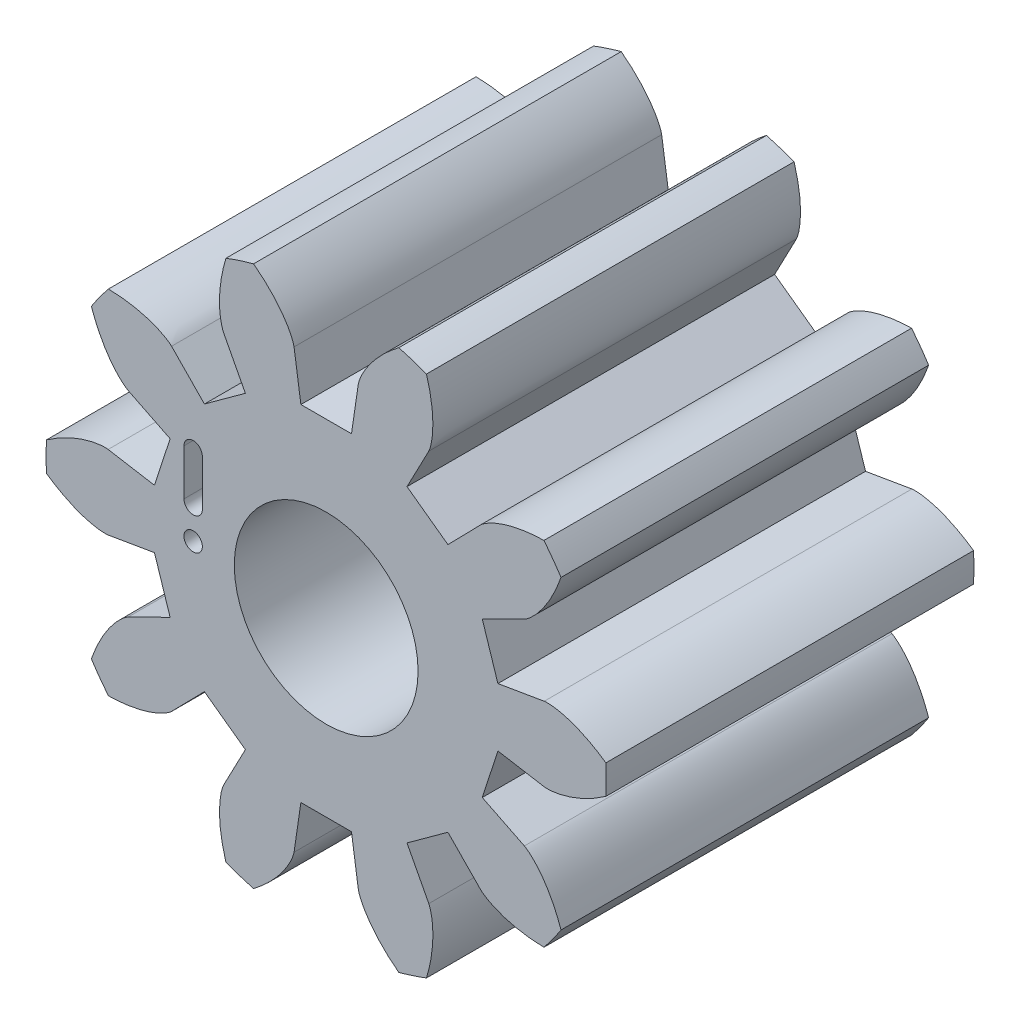
SolidWorks part; units mm, degrees
ref_plane "Front Plane" through (0, 0, 0) normal (0, 0, 1) x (1, 0, 0)
ref_plane "Top Plane" through (0, 0, 0) normal (0, 1, 0) x (1, 0, 0)
ref_plane "Right Plane" through (0, 0, 0) normal (1, 0, 0) x (0, 0, -1)
ref_axis "Axis1" through (0, 0, 4.2) along (0, 0, -1)
sketch "Sketch2" plane through (0, 0, 0) normal (0, 0, 1) x (1, 0, 0)
  circle A0 centre (0, 0) radius 3.0476
  dimension "D1" = 6.0951
extrude "Boss-Extrude1" add sketch "Sketch2" along normal blind 4
sketch "Sketch1" plane through (0, 0, 0) normal (0, 0, 1) x (1, 0, 0)
  line L1 (2.1564, 1.0683) -> (1.6982, 0.8413) construction
  line L3 (1.8683, 0.3175) -> (2.3725, 0.4032) construction
  line L4 (3.8854, 0) -> (4.3327, 0) construction
  line L8 (2.1564, 1.0683) -> (1.6982, 0.8413)
  line L9 (1.6982, 0.8413) -> (1.8683, 0.3175)
  line L10 (1.8683, 0.3175) -> (2.3725, 0.4032)
  circle A0 centre (0, 0) radius 1.8951 construction
  circle A1 centre (0, 0) radius 2.4065 construction
  circle A6 centre (0, 0) radius 3.0476 construction
  arc A7 (2.5994, 1.8069) -> (3.165, 0.0661) centre (0, 0) cw
  arc A8 (1.6982, 0.8413) -> (1.8683, 0.3175) centre (0, 0) cw construction
  circle A11 centre (0, 0) radius 3.0476 construction
  arc A12 (2.1564, 1.0683) -> (2.3725, 0.4032) centre (0, 0) cw construction
  spline S0 degree 4 poles (2.1564, 1.0683) (2.1596, 1.07) (2.1656, 1.0735) (2.1751, 1.0796) (2.1932, 1.0925) (2.2129, 1.1083) (2.2344, 1.1272) (2.2565, 1.1487) (2.2749, 1.1678) (2.2926, 1.1874) (2.3098, 1.2075) (2.3301, 1.2324) (2.3535, 1.2632) (2.3796, 1.3004) (2.4076, 1.344) (2.4345, 1.3898) (2.4596, 1.4361) (2.4833, 1.484) (2.505, 1.5313) (2.5258, 1.5816) (2.5441, 1.6286) (2.5626, 1.6825) (2.577, 1.7264) (2.5938, 1.7854) (2.6031, 1.8207) (2.6133, 1.8623) (2.6174, 1.881) (2.6199, 1.8925) knots 0 0 0 0 0 0.015084 0.028532 0.04661 0.092111 0.119476 0.146842 0.174209 0.201575 0.228941 0.256307 0.307035 0.361767 0.4165 0.471232 0.525964 0.580697 0.635429 0.690161 0.744894 0.799626 0.854358 0.909091 0.954545 1 1 1 1 1 construction
  spline S1 degree 4 poles (2.1564, 1.0683) (2.1596, 1.07) (2.1656, 1.0735) (2.1751, 1.0796) (2.1932, 1.0925) (2.2129, 1.1083) (2.2344, 1.1272) (2.2565, 1.1487) (2.2749, 1.1678) (2.2926, 1.1874) (2.3098, 1.2075) (2.3301, 1.2324) (2.3535, 1.2632) (2.3796, 1.3004) (2.4076, 1.344) (2.4345, 1.3898) (2.4596, 1.4361) (2.4833, 1.484) (2.505, 1.5313) (2.5258, 1.5816) (2.5441, 1.6286) (2.5626, 1.6825) (2.577, 1.7264) (2.5902, 1.7726) (2.5964, 1.7953) (2.5994, 1.8069) knots 0 0 0 0 0 0.015084 0.028532 0.04661 0.092111 0.119476 0.146842 0.174209 0.201575 0.228941 0.256307 0.307035 0.361767 0.4165 0.471232 0.525964 0.580697 0.635429 0.690161 0.744894 0.799626 0.854358 0.909091 0.909091 0.909091 0.909091 0.909091
  spline S2 degree 4 poles (2.3725, 0.4032) (2.3761, 0.4038) (2.383, 0.4044) (2.3942, 0.4051) (2.4165, 0.4053) (2.4417, 0.4041) (2.4702, 0.4014) (2.5007, 0.397) (2.5268, 0.3924) (2.5527, 0.387) (2.5784, 0.3808) (2.6095, 0.3725) (2.6465, 0.3614) (2.6895, 0.3466) (2.7378, 0.3279) (2.7865, 0.3066) (2.834, 0.2839) (2.8813, 0.259) (2.9266, 0.2335) (2.973, 0.2051) (3.0155, 0.1778) (3.0622, 0.1451) (3.0996, 0.1181) (3.1479, 0.0802) (3.1761, 0.0571) (3.2088, 0.0294) (3.2231, 0.0167) (3.2319, 0.0089) knots 0 0 0 0 0 0.015084 0.028532 0.04661 0.092111 0.119476 0.146842 0.174209 0.201575 0.228941 0.256307 0.307035 0.361767 0.4165 0.471232 0.525964 0.580697 0.635429 0.690161 0.744894 0.799626 0.854358 0.909091 0.954545 1 1 1 1 1 construction
  spline S3 degree 4 poles (2.3725, 0.4032) (2.3761, 0.4038) (2.383, 0.4044) (2.3942, 0.4051) (2.4165, 0.4053) (2.4417, 0.4041) (2.4702, 0.4014) (2.5007, 0.397) (2.5268, 0.3924) (2.5527, 0.387) (2.5784, 0.3808) (2.6095, 0.3725) (2.6465, 0.3614) (2.6895, 0.3466) (2.7378, 0.3279) (2.7865, 0.3066) (2.834, 0.2839) (2.8813, 0.259) (2.9266, 0.2335) (2.973, 0.2051) (3.0155, 0.1778) (3.0622, 0.1451) (3.0996, 0.1181) (3.1374, 0.0884) (3.1557, 0.0737) (3.165, 0.0661) knots 0 0 0 0 0 0.015084 0.028532 0.04661 0.092111 0.119476 0.146842 0.174209 0.201575 0.228941 0.256307 0.307035 0.361767 0.4165 0.471232 0.525964 0.580697 0.635429 0.690161 0.744894 0.799626 0.854358 0.909091 0.909091 0.909091 0.909091 0.909091
  dimension "D1" = 3.7902
  dimension "D2" = 4.8131
  dimension "D3" = 6.0951
  dimension "D4" = 6.0951
extrude "Cut-Extrude2" cut sketch "Sketch1" along normal through all
pattern_circular "CirPattern1" count 10 over 360 about axis through (0, 0, 4.2) along (0, 0, -1) of "Cut-Extrude2"
sketch "Sketch3" plane through (0, 0, 0) normal (0, 0, 1) x (1, 0, 0)
  circle A0 centre (0, 0) radius 1
  dimension "D1" = 2
extrude "Cut-Extrude3" cut sketch "Sketch3" along normal through all
sketch "Sketch4" plane through (0, 0, 0) normal (0, 0, 1) x (1, 0, 0)
  circle A0 centre (-1.4476, 0) radius 0.1
  spline S0 degree 1 poles (0, 0) (-1.4476, 0) knots 0 0 1 1 construction
  spline S1 degree 1 poles (0, 0) (-1.4476, 0) knots 0 0 1 1 construction
  dimension "D1" = 0.2
extrude "LocationCut" cut sketch "Sketch4" against normal through all both and the other way through all
sketch "Sketch5" [suppressed] plane through (0, 0, 0) normal (0, 0, 1) x (1, 0, 0)
  circle A0 centre (-0.4403, -1.3553) radius 0.1
  spline S0 degree 4 poles (0.0444, 0.1366) (0.0427, 0.1313) (0.0387, 0.1192) (0.0364, 0.112) (0.0216, 0.0664) (0.0029, 0.0091) (-0.0129, -0.0397) (-0.0535, -0.1648) (-0.0781, -0.2403) (-0.1122, -0.3454) (-0.1367, -0.4206) (-0.1626, -0.5004) (-0.1847, -0.5683) (-0.2079, -0.6399) (-0.2298, -0.7074) (-0.2509, -0.7721) (-0.2697, -0.83) (-0.287, -0.8833) (-0.3035, -0.9341) (-0.3206, -0.9868) (-0.3382, -1.0409) (-0.3537, -1.0887) (-0.3703, -1.1398) (-0.3839, -1.1816) (-0.4009, -1.2337) (-0.4134, -1.2722) (-0.4355, -1.3402) (-0.4438, -1.3658) (-0.4625, -1.4234) (-0.4697, -1.4456) (-0.4783, -1.4719) (-0.4812, -1.4811) (-0.4834, -1.4877) (-0.4845, -1.4911) knots 0 0 0 0 0 0.010417 0.020833 0.041667 0.083333 0.145671 0.208009 0.267342 0.324672 0.369982 0.413075 0.452591 0.497901 0.542139 0.581511 0.610383 0.640797 0.673373 0.705996 0.740957 0.77184 0.79428 0.826344 0.853073 0.883495 0.916667 0.947038 0.971084 0.985542 0.992771 1 1 1 1 1 construction
  spline S1 degree 4 poles (0, 0) (-0.0069, -0.0211) (-0.0204, -0.0628) (-0.0535, -0.1648) (-0.0781, -0.2403) (-0.1122, -0.3454) (-0.1367, -0.4206) (-0.1626, -0.5004) (-0.1847, -0.5683) (-0.2079, -0.6399) (-0.2298, -0.7074) (-0.2509, -0.7721) (-0.2697, -0.83) (-0.287, -0.8833) (-0.3035, -0.9341) (-0.3206, -0.9868) (-0.3382, -1.0409) (-0.3537, -1.0887) (-0.3703, -1.1398) (-0.3839, -1.1816) (-0.4009, -1.2337) (-0.4134, -1.2722) (-0.4299, -1.3231) (-0.4367, -1.344) (-0.4403, -1.3553) knots 0.083333 0.083333 0.083333 0.083333 0.083333 0.145671 0.208009 0.267342 0.324672 0.369982 0.413075 0.452591 0.497901 0.542139 0.581511 0.610383 0.640797 0.673373 0.705996 0.740957 0.77184 0.79428 0.826344 0.853073 0.883495 0.916667 0.916667 0.916667 0.916667 0.916667 construction
  dimension "D1" = 0.2
extrude "S2LocationCut" [suppressed] cut sketch "Sketch5" against normal through all both and the other way through all
sketch "Sketch6" [suppressed] plane through (0, 0, 0) normal (0, 0, 1) x (1, 0, 0)
  circle A0 centre (1.1528, -0.8376) radius 0.1
  spline S0 degree 4 poles (-0.1162, 0.0844) (-0.1123, 0.0816) (-0.1001, 0.0727) (-0.0972, 0.0706) (-0.0542, 0.0394) (-0.008, 0.0058) (0.038, -0.0276) (0.1475, -0.1072) (0.2176, -0.1581) (0.3138, -0.228) (0.3884, -0.2822) (0.4647, -0.3376) (0.5272, -0.383) (0.5888, -0.4278) (0.6415, -0.4661) (0.6953, -0.5052) (0.7461, -0.5421) (0.7915, -0.5751) (0.8356, -0.6071) (0.8793, -0.6389) (0.9216, -0.6696) (0.9631, -0.6998) (1.0029, -0.7287) (1.0349, -0.7519) (1.0719, -0.7788) (1.0978, -0.7976) (1.1431, -0.8305) (1.1645, -0.8461) (1.212, -0.8806) (1.229, -0.8929) (1.2544, -0.9114) (1.261, -0.9162) (1.2659, -0.9197) (1.2684, -0.9216) knots 0 0 0 0 0 0.010417 0.020833 0.041667 0.083333 0.14901 0.214686 0.279361 0.34003 0.394259 0.450635 0.487313 0.527902 0.568491 0.605347 0.641512 0.675567 0.699462 0.732706 0.768716 0.796045 0.822421 0.843371 0.867803 0.892235 0.916667 0.941265 0.9749 0.98745 0.993725 1 1 1 1 1 construction
  spline S1 degree 4 poles (0, 0) (0.0189, -0.0138) (0.0572, -0.0415) (0.1475, -0.1072) (0.2176, -0.1581) (0.3138, -0.228) (0.3884, -0.2822) (0.4647, -0.3376) (0.5272, -0.383) (0.5888, -0.4278) (0.6415, -0.4661) (0.6953, -0.5052) (0.7461, -0.5421) (0.7915, -0.5751) (0.8356, -0.6071) (0.8793, -0.6389) (0.9216, -0.6696) (0.9631, -0.6998) (1.0029, -0.7287) (1.0349, -0.7519) (1.0719, -0.7788) (1.0978, -0.7976) (1.1317, -0.8223) (1.1458, -0.8325) (1.1528, -0.8376) knots 0.083333 0.083333 0.083333 0.083333 0.083333 0.14901 0.214686 0.279361 0.34003 0.394259 0.450635 0.487313 0.527902 0.568491 0.605347 0.641512 0.675567 0.699462 0.732706 0.768716 0.796045 0.822421 0.843371 0.867803 0.892235 0.916667 0.916667 0.916667 0.916667 0.916667 construction
  dimension "D1" = 0.2
extrude "S3LocationCut" [suppressed] cut sketch "Sketch6" against normal through all both and the other way through all
sketch "Sketch7" plane through (0, 0, 4) normal (0, 0, 1) x (1, 0, 0)
  line L0 (-1.4476, 0.85) -> (-1.4476, 0.35) construction
  line L2 (-1.5476, 0.85) -> (-1.5476, 0.35)
  line L4 (-1.3476, 0.85) -> (-1.3476, 0.35)
  line L5 (-1.4476, 0.6) -> (-2.6866, 0.6) construction
  arc A0 (-1.5476, 0.85) -> (-1.3476, 0.85) centre (-1.4476, 0.85) cw
  arc A1 (-1.5476, 0.35) -> (-1.3476, 0.35) centre (-1.4476, 0.35) ccw
  spline S0 degree 1 poles (0, 0) (-1.4476, 0) knots 0 0 1 1 construction
  dimension "D1" = 0.2
  dimension "D2" = 0.5
  dimension "D3" = 0.6
extrude "Cut-Extrude4" cut sketch "Sketch7" against normal blind 0.2 and the other way through all
sketch "Sketch8" [suppressed] plane through (0, 0, 4) normal (0, 0, 1) x (1, 0, 0)
  line L0 (-0.9159, -1.2007) -> (-1.2012, -1.108) construction
  line L2 (-0.885, -1.1056) -> (-1.1703, -1.0129)
  line L4 (-0.9468, -1.2959) -> (-1.2321, -1.2031)
  line L5 (-1.3701, -2.1132) -> (-1.0585, -1.1544) construction
  line L6 (-1.0086, -1.4861) -> (-1.2939, -1.3934)
  line L7 (-1.0704, -1.6763) -> (-1.3557, -1.5836)
  line L8 (-1.0395, -1.5812) -> (-1.3248, -1.4885) construction
  arc A0 (-0.885, -1.1056) -> (-0.9468, -1.2959) centre (-0.9159, -1.2007) cw
  arc A1 (-1.1703, -1.0129) -> (-1.2321, -1.2031) centre (-1.2012, -1.108) ccw
  arc A2 (-1.0086, -1.4861) -> (-1.0704, -1.6763) centre (-1.0395, -1.5812) cw
  arc A3 (-1.2939, -1.3934) -> (-1.3557, -1.5836) centre (-1.3248, -1.4885) ccw
  spline S0 degree 4 poles (0, 0) (-0.0069, -0.0211) (-0.0204, -0.0628) (-0.0535, -0.1648) (-0.0781, -0.2403) (-0.1122, -0.3454) (-0.1367, -0.4206) (-0.1626, -0.5004) (-0.1847, -0.5683) (-0.2079, -0.6399) (-0.2298, -0.7074) (-0.2509, -0.7721) (-0.2697, -0.83) (-0.287, -0.8833) (-0.3035, -0.9341) (-0.3206, -0.9868) (-0.3382, -1.0409) (-0.3537, -1.0887) (-0.3703, -1.1398) (-0.3839, -1.1816) (-0.4009, -1.2337) (-0.4134, -1.2722) (-0.4299, -1.3231) (-0.4367, -1.344) (-0.4403, -1.3553) knots 0.083333 0.083333 0.083333 0.083333 0.083333 0.145671 0.208009 0.267342 0.324672 0.369982 0.413075 0.452591 0.497901 0.542139 0.581511 0.610383 0.640797 0.673373 0.705996 0.740957 0.77184 0.79428 0.826344 0.853073 0.883495 0.916667 0.916667 0.916667 0.916667 0.916667 construction
  dimension "D1" = 0.2
  dimension "D2" = 0.3
  dimension "D4" = 0.5
  dimension "D5" = 0.4
  dimension "D3" = 2
extrude "Cut-Extrude5" [suppressed] cut sketch "Sketch8" against normal blind 0.5
sketch "Sketch9" [suppressed] plane through (0, 0, 4) normal (0, 0, 1) x (1, 0, 0)
  line L0 (0.712, -1.4444) -> (1.0059, -1.0398) construction
  line L1 (0.7929, -1.5031) -> (1.0868, -1.0986)
  line L3 (0.6311, -1.3856) -> (0.925, -0.9811)
  line L4 (0.859, -1.2421) -> (0.7858, -1.189) construction
  line L5 (1.0356, -1.6795) -> (1.3295, -1.275)
  line L6 (0.8738, -1.5619) -> (1.1677, -1.1574)
  line L7 (0.9547, -1.6207) -> (1.2486, -1.2162) construction
  line L8 (0.5502, -1.3268) -> (0.8441, -0.9223)
  line L9 (0.3884, -1.2092) -> (0.6823, -0.8047)
  line L10 (0.4693, -1.268) -> (0.7632, -0.8635) construction
  line L11 (0.9547, -1.6207) -> (1.0356, -1.6795) construction
  line L12 (0.712, -1.4444) -> (0.7929, -1.5031) construction
  line L13 (0.4693, -1.268) -> (0.5502, -1.3268) construction
  line L14 (0.4693, -1.268) -> (0.712, -1.4444) construction
  line L15 (0.712, -1.4444) -> (0.9547, -1.6207) construction
  arc A0 (0.6311, -1.3856) -> (0.7929, -1.5031) centre (0.712, -1.4444) ccw
  arc A1 (0.925, -0.9811) -> (1.0868, -1.0986) centre (1.0059, -1.0398) cw
  arc A2 (0.8738, -1.5619) -> (1.0356, -1.6795) centre (0.9547, -1.6207) ccw
  arc A3 (1.1677, -1.1574) -> (1.3295, -1.275) centre (1.2486, -1.2162) cw
  arc A4 (0.3884, -1.2092) -> (0.5502, -1.3268) centre (0.4693, -1.268) ccw
  arc A5 (0.6823, -0.8047) -> (0.8441, -0.9223) centre (0.7632, -0.8635) cw
  spline S0 degree 4 poles (0, 0) (0.0189, -0.0138) (0.0572, -0.0415) (0.1475, -0.1072) (0.2176, -0.1581) (0.3138, -0.228) (0.3884, -0.2822) (0.4647, -0.3376) (0.5272, -0.383) (0.5888, -0.4278) (0.6415, -0.4661) (0.6953, -0.5052) (0.7461, -0.5421) (0.7915, -0.5751) (0.8356, -0.6071) (0.8793, -0.6389) (0.9216, -0.6696) (0.9631, -0.6998) (1.0029, -0.7287) (1.0349, -0.7519) (1.0719, -0.7788) (1.0978, -0.7976) (1.1317, -0.8223) (1.1458, -0.8325) (1.1528, -0.8376) knots 0.083333 0.083333 0.083333 0.083333 0.083333 0.14901 0.214686 0.279361 0.34003 0.394259 0.450635 0.487313 0.527902 0.568491 0.605347 0.641512 0.675567 0.699462 0.732706 0.768716 0.796045 0.822421 0.843371 0.867803 0.892235 0.916667 0.916667 0.916667 0.916667 0.916667 construction
  dimension "D1" = 0.3
  dimension "D2" = 0.2
  dimension "D5" = 0.5
  dimension "D3" = 0.5
extrude "Cut-Extrude6" [suppressed] cut sketch "Sketch9" against normal blind 0.3
equation "\"R1_NumTeeth\"= 52"
equation "\"R2_teeth\"= 51"
equation "\"P1_teeth\"= 10"
equation "\"sun_teeth\"= \"R1_NumTeeth\" - 2 * \"P1_teeth\""
equation "\"S2_Module\"= 0.5121951219512195\t\t\t'stage two gear modules CAN be different from stage 1; this makes things a lot more complicated though so try and avoid it if you can"
equation "\"P2_teeth\" = 10"
equation "\"Nteeth\"= \"P2_teeth\""
equation "\"S1_Module\"= 0.5\t\t'tooth per mm"
equation "\"module\" = \"S2_Module\""
equation "\"S1_PressureAngle\"= 20'deg. leave unitless"
equation "\"pressure_angle\"= \"S1_PressureAngle\" * pi / 180"
equation "\"Planet_profile_shift\" = -0.05"
equation "\"x_shift\"= \"Planet_profile_shift\""
equation "\"r_p\"= \"module\" * \"Nteeth\" / 2'pitch circle radius"
equation "\"r_b\"= \"r_p\" * cos ( \"pressure_angle\" )'base circle radius"
equation "\"r_a\"= \"r_p\" + \"module\" * ( 1 + \"x_shift\" )'addendum"
equation "\"r_f\"= \"r_p\" - \"module\" * ( 1.25 - \"x_shift\" )'dedendum"
equation "\"tmax\"= sqr ( ( \"r_a\" / \"r_b\" ) * ( \"r_a\" / \"r_b\" ) - 1 ) * 1.1"
equation "\"t_p\"= sqr ( ( \"r_p\" / \"r_b\" ) ^ 2 - 1 )'t at pitch circle"
equation "\"x_p\"= \"r_b\" * ( cos ( \"t_p\" ) + \"t_p\" * sin ( \"t_p\" ) )"
equation "\"y_p\"= \"r_b\" * ( sin ( \"t_p\" ) - \"t_p\" * cos ( \"t_p\" ) )"
equation "\"theta_p\"= atn ( \"y_p\" / \"x_p\" )"
equation "\"des_ang\"= ( pi / 2 - 2 * \"x_shift\" * tan ( \"pressure_angle\" ) ) / \"Nteeth\""
equation "\"delta\"= \"des_ang\" - \"theta_p\""
equation "\"delta2\"= \"delta\" + 2 * pi * ( \"Nteeth\" - 1 ) / \"Nteeth\""
equation "\"height\"=4"
equation "\"Planet_broachcutter_offset\" = -0.0"
equation "\"fillet\"= 0.1 'radius of the fillet at the base of the tooth near the dedendum"
equation "\"halftooth\"= pi / \"Nteeth\""
equation "\"S1_carrier_radius\"= \"P1_teeth\" * \"S1_Module\" / 2  + \"sun_teeth\" * \"S1_Module\" / 2"
equation "\"S2_PressureAngle\"= \"S1_PressureAngle\"'stage two pressure angle can be different, but for simplicity keep it the same"
equation "\"Ring_profile_shift\" = 0.05"
equation "\"Ring_broachcutter_offset\" = 0.0"
equation "\"Nteeth_bcg\"= \"P2_teeth\""
equation "\"r_p_bcg\"= \"module\" * \"Nteeth_bcg\" / 2"
equation "\"r_a_bcg\"= \"r_p_bcg\" + \"module\" * ( 1 + \"x_shift\" )"
equation "\"r_f_bcg\"= \"r_p_bcg\" - \"module\" * ( 1.25 - \"x_shift\" )"
equation "\"involute_offset\"= - \"r_a\" + \"r_a_bcg\" + \"Planet_broachcutter_offset\""
equation "\"D1@Sketch2\"=(\"r_a\"+\"involute_offset\")*2"
equation "\"D2@Sketch1\"=(\"r_b\"+\"involute_offset\")*2"
equation "\"D4@Sketch1\"=(\"r_a\"+\"involute_offset\")*2"
equation "\"D1@Sketch1\"=(\"r_f\"+\"involute_offset\")*2"
equation "\"Bore\"= 2'center bore diameter"
equation "\"D1@Sketch3\"=\"Bore\""
equation "\"D1@CirPattern1\"=\"Nteeth_bcg\""
equation "\"D1@Boss-Extrude1\"=\"height\""
equation "\"D3@Sketch1\"=\"r_a\"*2"
equation "\"invrot\"= ( ( 2 * pi ) / \"Nteeth\" ) / 2"
